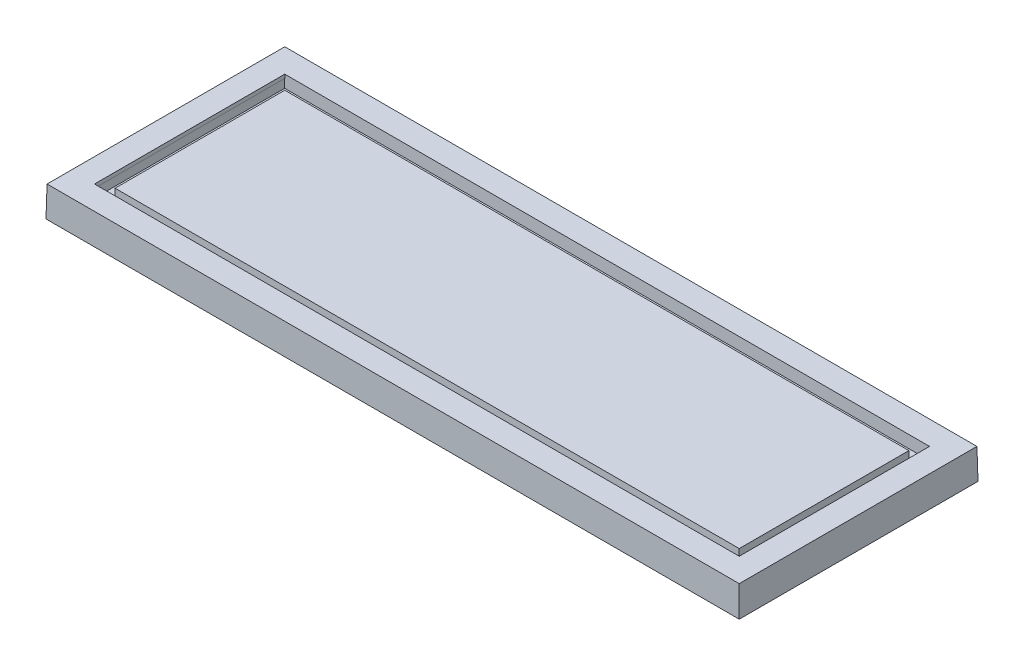
SolidWorks part; units mm, degrees
ref_plane "Front Plane" through (0, 0, 0) normal (0, 0, 1) x (1, 0, 0)
ref_plane "Top Plane" through (0, 0, 0) normal (0, 1, 0) x (1, 0, 0)
ref_plane "Right Plane" through (0, 0, 0) normal (1, 0, 0) x (0, 0, -1)
sketch "Sketch1" plane through (0, 0, 0) normal (0, 1, 0) x (1, 0, 0)
  line L1 (-286, -98.5) -> (286, -98.5)
  line L2 (-286, -98.5) -> (-286, 98.5)
  line L3 (-286, 98.5) -> (286, 98.5)
  line L4 (286, -98.5) -> (286, 98.5)
  line L5 (-286, -98.5) -> (286, 98.5) construction
  line L6 (-286, 98.5) -> (286, -98.5) construction
  point P0 (0, 0)
  dimension "D1" = 572
  dimension "D2" = 197
extrude "Boss-Extrude1" add sketch "Sketch1" along normal blind 25 draft 1
sketch "Sketch2" plane through (0, 25, 0) normal (0, 1, 0) x (1, 0, 0)
  line L1 (-266, -78.5) -> (266, -78.5)
  line L2 (-266, -78.5) -> (-266, 78.5)
  line L3 (-266, 78.5) -> (266, 78.5)
  line L4 (266, -78.5) -> (266, 78.5)
  line L5 (-266, -78.5) -> (266, 78.5) construction
  line L6 (-266, 78.5) -> (266, -78.5) construction
  point P0 (0, 0)
  dimension "D1" = 532
  dimension "D2" = 157
extrude "Cut-Extrude1" cut sketch "Sketch2" against normal blind 3 draft 1
sketch "Sketch4" plane through (0, 22, 0) normal (0, 1, 0) x (1, 0, 0)
  line L0 (266, 78.5) -> (-266, 78.5) construction
  line L1 (-257.5, -70) -> (257.5, -70)
  line L2 (-257.5, -70) -> (-257.5, 70)
  line L3 (-257.5, 70) -> (257.5, 70)
  line L4 (257.5, -70) -> (257.5, 70)
  line L5 (-257.5, -70) -> (257.5, 70) construction
  line L6 (-257.5, 70) -> (257.5, -70) construction
  line L7 (-266, 78.5) -> (-266, -78.5) construction
  line L8 (265.9476, 78.4476) -> (-265.9476, 78.4476) construction
  line L9 (-266, -78.4476) -> (266, -78.4476)
  line L10 (-266, -78.4476) -> (-266, 78.4476)
  line L11 (-266, 78.4476) -> (266, 78.4476)
  line L12 (266, -78.4476) -> (266, 78.4476)
  line L13 (-266, -78.4476) -> (266, 78.4476) construction
  line L14 (-266, 78.4476) -> (266, -78.4476) construction
  point P1 (0, 0)
  point P8 (-257.5, 0)
  point P11 (0, 0)
  dimension "D1" = 8.5
  dimension "D2" = 8.5
  dimension "D3" = 532
  dimension "D4" = 156.8953
extrude "Cut-Extrude2" cut sketch "Sketch4" against normal blind 7 draft 1
ref_plane "Plane2" through (-257.6222, 15, -70.1222) normal (0, 0, 1) x (1, 0, 0)
